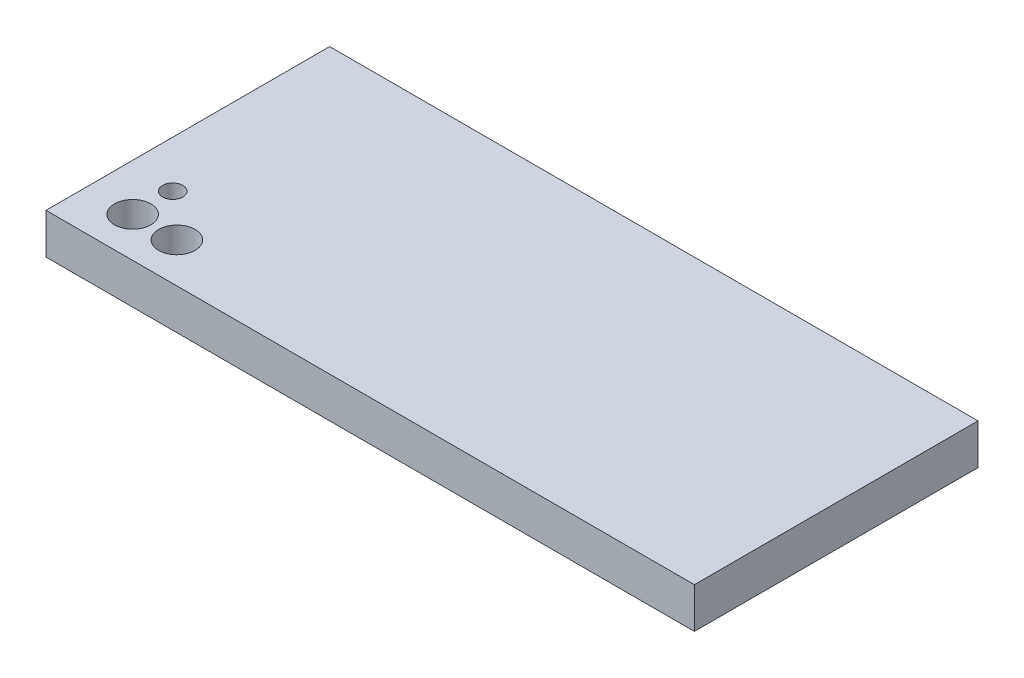
SolidWorks part; units mm, degrees
ref_plane "Front Plane" through (0, 0, 0) normal (0, 0, 1) x (1, 0, 0)
ref_plane "Top Plane" through (0, 0, 0) normal (0, 1, 0) x (1, 0, 0)
ref_plane "Right Plane" through (0, 0, 0) normal (1, 0, 0) x (0, 0, -1)
sketch "Sketch1" plane through (0, 0, 0) normal (0, 1, 0) x (1, 0, 0)
  line L0 (-80, -35) -> (-68.4461, -35) construction
  line L1 (-80, 35) -> (80, 35)
  line L2 (-80, 35) -> (-80, -35)
  line L3 (-80, -35) -> (80, -35)
  line L4 (80, 35) -> (80, -35)
  line L5 (-80, 35) -> (80, -35) construction
  line L6 (-80, -35) -> (80, 35) construction
  line L7 (-68.4461, -35) -> (-68.4461, -25.1699) construction
  line L8 (-68.4461, -25.1699) -> (-68.4461, -15.2837) construction
  line L9 (-68.4461, -25.1699) -> (-57.5312, -25.1699) construction
  circle A0 centre (-68.4461, -25.1699) radius 4.5
  circle A1 centre (-68.4461, -15.2837) radius 2.5
  circle A2 centre (-57.5312, -25.1699) radius 4.5
  point P0 (0, 0)
extrude "Boss-Extrude1" add sketch "Sketch1" against normal blind 10
